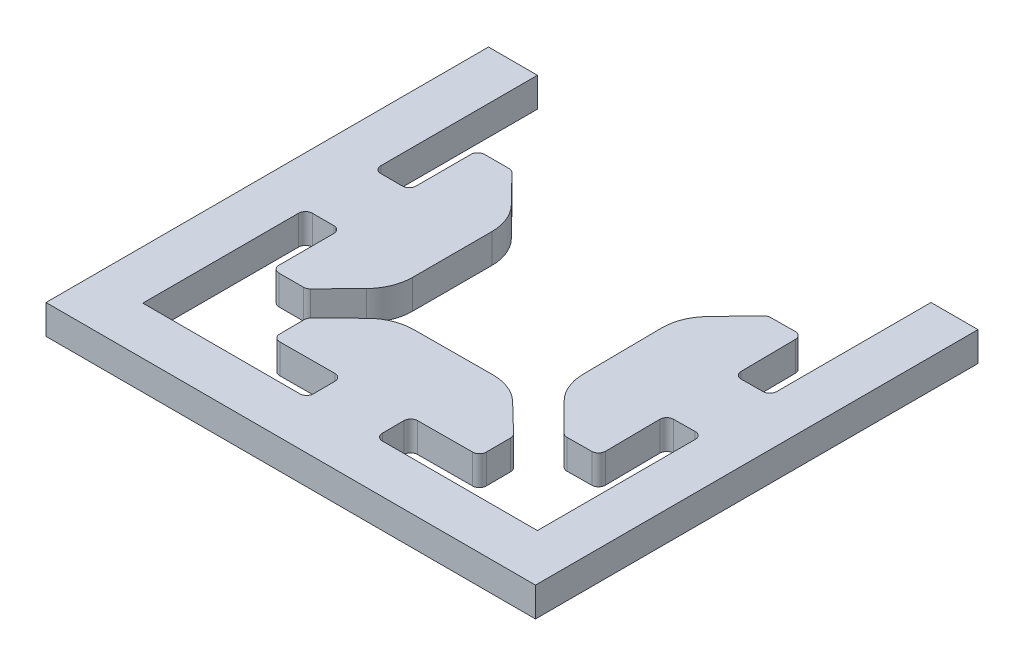
SolidWorks part; units mm, degrees
ref_plane "Front Plane" through (0, 0, 0) normal (0, 0, 1) x (1, 0, 0)
ref_plane "Top Plane" through (0, 0, 0) normal (0, 1, 0) x (1, 0, 0)
ref_plane "Right Plane" through (0, 0, 0) normal (1, 0, 0) x (0, 0, -1)
sketch "Sketch1" plane through (0, 0, 0) normal (0, 1, 0) x (1, 0, 0)
  line L1 (-25, -25) -> (25, -25)
  line L2 (-25, -25) -> (-25, 20.2)
  line L4 (25, -25) -> (25, 20.2)
  line L5 (-25, -25) -> (20.2, 20.2) construction
  line L6 (-20, 20.2) -> (25, -25) construction
  line L8 (-20, -20.115) -> (-20, -3.5)
  line L9 (-20, 20.2) -> (20.2, 20.2)
  line L11 (-20, -20.115) -> (20.2, 20.2) construction
  line L12 (-20, 20.2) -> (20.2722, -20.0789) construction
  line L13 (-20, 3.5) -> (-16.4, 3.5)
  line L14 (-16.4, 3.5) -> (-16.4, 10.5)
  line L16 (-8.5, 6) -> (-8.5, -6)
  line L20 (-20, 20.2) -> (-25, 20.2)
  line L21 (20.2, 20.2) -> (25, 20.2)
  line L22 (-20, 3.5) -> (-20, 20.2)
  line L23 (3.7437, -20.0789) -> (20.2722, -20.0789)
  line L24 (20.2, 3.75) -> (20.2, 20.2)
  line L25 (-8.5, 6) -> (-12.9, 10.5)
  line L26 (-12.9, 10.5) -> (-16.4, 10.5)
  line L27 (-55, 0) -> (55, 0) construction
  line L28 (-8.5, -6) -> (-12.9, -10.5)
  line L29 (-12.9, -10.5) -> (-16.4, -10.5)
  line L30 (-3.2562, -20.115) -> (-3.2747, -16.515)
  line L31 (-3.2747, -16.515) -> (-10.2746, -16.5511)
  line L32 (-5.8154, -8.628) -> (-10.2927, -13.0511)
  line L33 (-10.2927, -13.0511) -> (-10.2746, -16.5511)
  line L34 (-5.8154, -8.628) -> (6.1844, -8.5661)
  line L35 (6.1844, -8.5661) -> (10.707, -12.9429)
  line L36 (10.707, -12.9429) -> (10.7251, -16.4428)
  line L37 (3.7252, -16.4789) -> (10.7251, -16.4428)
  line L38 (3.7437, -20.0789) -> (3.7252, -16.4789)
  line L39 (20.2722, -3.2496) -> (16.6724, -3.2867)
  line L40 (16.6724, -3.2867) -> (16.7445, -10.2864)
  line L41 (8.7986, -5.8681) -> (13.2447, -10.3225)
  line L42 (13.2447, -10.3225) -> (16.7445, -10.2864)
  line L43 (8.7986, -5.8681) -> (8.6748, 6.1313)
  line L45 (8.6748, 6.1313) -> (13.0282, 10.6764)
  line L46 (13.0282, 10.6764) -> (16.528, 10.7125)
  line L48 (16.6002, 3.7129) -> (16.528, 10.7125)
  line L51 (-16.4, -3.5) -> (-16.4, -10.5)
  line L52 (-20, -3.5) -> (-16.4, -3.5)
  line L53 (20.2, 3.75) -> (16.6002, 3.7129)
  line L54 (20.2722, -3.2496) -> (20.2722, -20.0789)
  line L55 (-3.2562, -20.115) -> (-20, -20.115)
  point P0 (0, 0)
  point P5 (0, 0)
  point P21 (-8.5, 0)
  point P47 (0, 0)
  dimension "D1" = 50
  dimension "D2" = 7
  dimension "D3" = 5
  dimension "D4" = 12
  dimension "D5" = 3
  dimension "D6" = 11.5
  dimension "D8" = 7.9
  dimension "D9" = 7
  dimension "D10" = 3.5
extrude "Boss-Extrude1" add sketch "Sketch1" along normal blind 3
fillet "Fillet4" radius 0.7 24 edges at (-16.4, 1.5, -3.5) (-20, 1.5, -3.5) (-12.9, 1.5, 10.5) (-16.4, 1.5, 10.5) (-20, 1.5, 3.5) (-16.4, 1.5, 3.5) (-12.9, 1.5, -10.5) (-16.4, 1.5, -10.5) (20.2, 1.5, -3.75) (16.6002, 1.5, -3.7129) (16.528, 1.5, -10.7125) (13.0282, 1.5, -10.6764) (3.7437, 1.5, 20.0789) (3.7252, 1.5, 16.4789) (10.7251, 1.5, 16.4428) (10.707, 1.5, 12.9429) (16.6724, 1.5, 3.2867) (20.2722, 1.5, 3.2496) (16.7445, 1.5, 10.2864) (13.2447, 1.5, 10.3225) (-3.2747, 1.5, 16.515) (-3.2562, 1.5, 20.115) (-10.2746, 1.5, 16.5511) (-10.2927, 1.5, 13.0511)
fillet "Fillet5" radius 4.8 6 edges at (-8.5, 1.5, 6) (-8.5, 1.5, -6) (8.7986, 1.5, 5.8681) (8.6748, 1.5, -6.1313) (6.1844, 1.5, 8.5661) (-5.8154, 1.5, 8.628)
